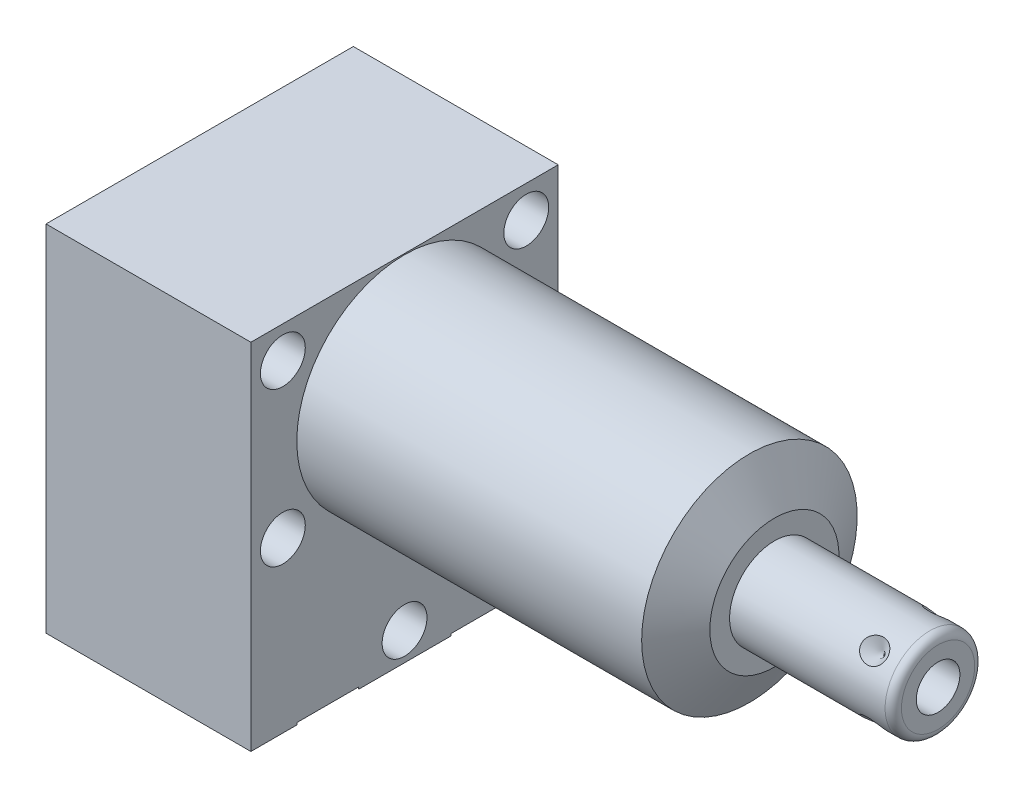
SolidWorks part; units mm, degrees
material "Alloy Steel"
ref_plane "Front Plane" through (0, 0, 0) normal (0, 0, 1) x (1, 0, 0)
ref_plane "Top Plane" through (0, 0, 0) normal (0, 1, 0) x (1, 0, 0)
ref_plane "Right Plane" through (0, 0, 0) normal (1, 0, 0) x (0, 0, -1)
ref_plane "Plane1" through (0, 0, 0) normal (1, 0, 0) x (0, 0, -1)
sketch "Sketch1" plane through (0, 0, 0) normal (1, 0, 0) x (0, 0, -1)
  line L0 (-19.05, 13.4874) -> (-19.05, -30.4546)
  line L1 (-19.05, -30.4546) -> (19.05, -30.4546)
  line L2 (19.05, -30.4546) -> (19.05, 13.4874)
  line L3 (19.05, 13.4874) -> (-19.05, 13.4874)
  line L4 (0, -32.6517) -> (0, 15.6845) construction
  dimension "D1" = 38.1
  dimension "D2" = 43.942
  dimension "D3" = 13.4874
extrude "Extrude1" add sketch "Sketch1" along normal blind 45.847 and the other way blind 25.4
ref_plane "Plane2" through (0, 0, 0) normal (1, 0, 0) x (0, 0, -1)
sketch "Sketch2" plane through (0, 0, 0) normal (1, 0, 0) x (0, 0, -1)
  line L0 (-14.6964, 0) -> (14.6964, 0) construction
  line L5 (19.05, 13.4874) -> (-19.05, 13.4874)
  line L6 (-19.05, 13.4874) -> (-19.05, -30.4546)
  line L7 (-19.05, -30.4546) -> (19.05, -30.4546)
  line L8 (19.05, -30.4546) -> (19.05, 13.4874)
  line L9 (19.05, 13.4874) -> (-19.05, 13.4874)
  line L10 (-19.05, 13.4874) -> (-19.05, -30.4546)
  line L11 (-19.05, -30.4546) -> (19.05, -30.4546)
  line L12 (19.05, -30.4546) -> (19.05, 13.4874)
  circle A0 centre (0, 0) radius 13.3604
  dimension "D1" = 26.7208
  dimension "D2" = 0
extrude "Cut-Extrude1" cut sketch "Sketch2" along normal up to next
ref_plane "Plane3" through (0, 0, 0) normal (0, 0, 1) x (1, 0, 0)
sketch "Sketch3" plane through (0, 0, 0) normal (0, 0, 1) x (1, 0, 0)
  line L0 (42.7527, 13.3604) -> (45.847, 8.001)
  line L1 (42.598, 0) -> (46.0017, 0) construction
  line L2 (45.847, 13.3604) -> (45.847, 8.001)
  line L3 (45.847, 13.3604) -> (42.7527, 13.3604)
  line L4 (45.847, 13.3604) -> (0, 13.3604) construction
  line L5 (45.847, -13.3604) -> (45.847, 13.3604) construction
  dimension "D1" = 30
  dimension "D2" = 16.002
revolve "Cut-Revolve1" cut sketch "Sketch3" angle 360 about L1
ref_plane "Plane4" through (-22.733, -19.8374, 9.525) normal (0, 0, 1) x (0, 1, 0)
sketch "S2D0002" plane through (-22.733, -19.8374, 9.525) normal (0, 0, 1) x (0, 1, 0)
  line L0 (-0.8128, 0) -> (3.7338, 0)
  line L1 (3.7338, 0) -> (3.2938, -2.0701)
  line L2 (3.2938, -2.0701) -> (2.6416, -2.7223)
  line L3 (2.6416, -2.7223) -> (2.6416, -13.97)
  line L4 (2.6416, -13.97) -> (-0.8128, -13.97)
  line L5 (-0.8128, -13.97) -> (-0.8128, 0)
  line L6 (-0.8128, -14.6685) -> (-0.8128, 0.6985) construction
  line L7 (19.8374, -65.4857) -> (19.8374, -22.733) construction
  dimension "D1" = 13.97
  dimension "D2" = 20.6502
revolve "Cut-Revolve2" cut sketch "S2D0002" angle 360 about L6
ref_plane "Plane5" through (-22.733, -19.8374, -9.525) normal (0, 0, 1) x (0, 1, 0)
sketch "Sketch5" plane through (-22.733, -19.8374, -9.525) normal (0, 0, 1) x (0, 1, 0)
  line L0 (-0.8128, 0) -> (3.7338, 0)
  line L1 (3.7338, 0) -> (3.2938, -2.0701)
  line L2 (3.2938, -2.0701) -> (2.6416, -2.7223)
  line L3 (2.6416, -2.7223) -> (2.6416, -13.97)
  line L4 (2.6416, -13.97) -> (-0.8128, -13.97)
  line L5 (-0.8128, -13.97) -> (-0.8128, 0)
  line L6 (-0.8128, -14.6685) -> (-0.8128, 0.6985) construction
  line L7 (19.8374, -65.4857) -> (19.8374, -22.733) construction
  dimension "D1" = 13.97
  dimension "D2" = 20.6502
revolve "Cut-Revolve3" cut sketch "Sketch5" angle 360 about L6
ref_plane "Plane6" through (-8.7376, -30.2006, 9.525) normal (0, 0, 1) x (-1, 0, 0)
sketch "Sketch14" plane through (-25.4, 0, 0) normal (-1, 0, 0) x (0, 0, 1)
  circle A0 centre (-9.525, -20.6502) radius 7.9375
  circle A1 centre (9.525, -20.6502) radius 7.9375
  dimension "D1" = 15.875
extrude "Cut-Extrude2" cut sketch "Sketch14" against normal blind 2.667
sketch "Sketch6" plane through (-8.7376, -30.2006, 9.525) normal (0, 0, 1) x (-1, 0, 0)
  line L0 (16.6624, -43.688) -> (16.6624, 0.254) construction
  line L1 (6.1836, 0) -> (5.641, -2.5527)
  line L2 (5.641, -2.5527) -> (4.9771, -3.2166)
  line L3 (4.9771, -3.2166) -> (4.9771, -17.272)
  line L4 (4.9771, -17.272) -> (0, -17.272)
  line L5 (0, -17.272) -> (0, 0)
  line L6 (0, -18.1356) -> (0, 0.8636) construction
  line L7 (6.1836, 0) -> (9.5237, 0)
  line L8 (9.5237, 0) -> (9.5237, 0.254)
  line L9 (16.6624, 0.254) -> (-8.7376, 0.254) construction
  line L10 (9.5237, 0.254) -> (0, 0.254)
  line L11 (0, 0.254) -> (0, 0)
  dimension "D1" = 19.0475
  dimension "D2" = 0.254
  dimension "D3" = 16.6624
revolve "Cut-Revolve4" cut sketch "Sketch6" angle 360 about L6
ref_plane "Plane7" through (-8.7376, -30.2006, -9.525) normal (0, 0, 1) x (-1, 0, 0)
sketch "Sketch7" plane through (-8.7376, -30.2006, -9.525) normal (0, 0, 1) x (-1, 0, 0)
  line L0 (16.6624, -43.688) -> (16.6624, 0.254) construction
  line L1 (6.1849, 0) -> (5.6423, -2.5527)
  line L2 (5.6423, -2.5527) -> (4.9784, -3.2166)
  line L3 (4.9784, -3.2166) -> (4.9784, -17.272)
  line L4 (4.9784, -17.272) -> (0, -17.272)
  line L5 (0, -17.272) -> (0, 0)
  line L6 (0, -18.1356) -> (0, 0.8636) construction
  line L7 (6.1849, 0) -> (9.5237, 0)
  line L8 (9.5237, 0) -> (-8.7376, 0) construction
  line L9 (9.5237, 0) -> (9.5237, 0.254)
  line L10 (16.6624, 0.254) -> (-8.7376, 0.254) construction
  line L11 (9.5237, 0.254) -> (0, 0.254)
  line L12 (0, 0.254) -> (0, 0)
  dimension "D1" = 16.6624
  dimension "D2" = 9.9568
  dimension "D3" = 19.0475
revolve "Cut-Revolve5" cut sketch "Sketch7" angle 360 about L6
ref_plane "Plane8" through (0, 0, 0) normal (0, 0, 1) x (1, 0, 0)
sketch "Sketch8" plane through (0, 0, 0) normal (0, 0, 1) x (1, 0, 0)
  line L0 (45.847, 0) -> (45.847, 5.5562)
  line L1 (45.847, 5.5562) -> (65.1256, 5.5562)
  line L2 (66.1416, 4.5403) -> (66.1416, 0)
  line L3 (66.1416, 0) -> (45.847, 0)
  line L4 (44.8323, 0) -> (67.1563, 0) construction
  line L5 (45.847, -8.001) -> (45.847, 8.001) construction
  line L6 (-25.4, 13.4874) -> (-25.4, -30.4546) construction
  arc A0 (66.1416, 4.5403) -> (65.1256, 5.5562) centre (65.1256, 4.5403) ccw
  point P0 (45.847, 0)
  dimension "D3" = 1.016
  dimension "D1" = 91.5416
  dimension "D2" = 11.1125
revolve "Revolve1" add sketch "Sketch8" angle 360 about L4
ref_plane "Plane9" through (66.1416, -2.8067, 0) normal (0, 0, 1) x (0, -1, 0)
sketch "S2D0001" plane through (66.1416, -2.8067, 0) normal (0, 0, 1) x (0, -1, 0)
  line L0 (-0.1016, 0) -> (-0.1016, -9.652)
  line L1 (-0.1016, -9.652) -> (-2.8067, -11.2774)
  line L2 (-0.1016, 0) -> (-2.8067, 0)
  line L3 (-2.8067, 0) -> (-2.8067, -11.2774)
  line L4 (-2.8067, -12.4388) -> (-2.8067, 0.5923) construction
  line L5 (1.7335, 0) -> (-7.3469, 0) construction
  dimension "D1" = 5.4102
  dimension "D2" = 9.652
  dimension "D3" = 59
revolve "Cut-Revolve6" cut sketch "S2D0001" angle 360 about L4
ref_plane "Plane10" through (-25.4, -30.2006, 0) normal (0, -1, 0) x (0, 0, -1)
sketch "Sketch10" plane through (-25.4, -30.2006, 0) normal (0, -1, 0) x (0, 0, -1)
  circle A0 centre (-9.525, 16.6624) radius 6.4389
  circle A1 centre (-9.525, 16.6624) radius 6.1836 construction
  dimension "D1" = 12.8778
extrude "Extrude2" add sketch "Sketch10" along normal blind 1.651
sketch "Sketch11" plane through (-22.733, 0, 0) normal (-1, 0, 0) x (0, 0, 1)
  circle A0 centre (9.525, -20.6502) radius 4.8006
  circle A1 centre (9.525, -20.6502) radius 4.5466 construction
  dimension "D1" = 9.6012
ref_plane "Plane11" through (-25.4, 0, 0) normal (1, 0, 0) x (0, 0, -1)
extrude "Extrude3" add sketch "Sketch11" along normal up to surface (2.667 mm away) up to plane "Plane11"
ref_plane "Plane12" through (62.1792, -5.5562, 0) normal (0, 0, 1) x (-1, 0, 0)
ref_plane "Plane13" through (0, 0, 0) normal (0, 0.7071, 0.7071) x (-1, 0, 0)
sketch "Sketch12" plane through (62.1792, 3.9289, -3.9289) normal (0, -0.7071, -0.7071) x (-1, 0, 0)
  line L0 (0, 0) -> (1.5875, 0)
  line L1 (1.5875, 0) -> (0, -1.5875)
  line L2 (0, 0) -> (0, -1.5875)
  line L3 (0, -3.434) -> (0, 0.0794) construction
  line L4 (16.3322, 0) -> (-2.9464, 0) construction
  line L5 (-3.9624, -1.016) -> (-3.9624, -10.0965) construction
  dimension "D1" = 3.9624
  dimension "D2" = 45
  dimension "D3" = 3.175
revolve "Cut-Revolve7" cut sketch "Sketch12" angle 360 about L3
pattern_circular "CirPattern1" count 4 over 360 about axis through (45.848, 0, 0) along (-1, 0, 0) of "Cut-Revolve7"
hole_wizard "Hole1" positions "Sketch17" profile "Sketch16" legacy end condition up to next
sketch "Sketch17" plane through (0, 0, 0) normal (1, 0, 0) x (0, 0, -1)
  line L0 (0, 0) -> (0, 17.9298) construction
  line L1 (0, 0) -> (-24.6425, 0) construction
  point P0 (-15.0876, 9.525)
  point P10 (-15.0876, -9.525)
  point P12 (15.0876, 9.525)
  point P13 (15.0876, -9.525)
  point P14 (0, -26.9748)
  dimension "D1" = 9.525
  dimension "D2" = 15.0876
  dimension "D3" = 26.9748
sketch "Sketch16" plane through (0, 9.525, 15.0876) normal (0, 1, 0) x (0, 0, -1)
  line L0 (0, 0) -> (0, 25.4)
  line L1 (0, 25.4) -> (2.7813, 25.4)
  line L2 (2.7813, 25.4) -> (2.7813, 0)
  line L3 (2.7813, 0) -> (0, 0)
  line L4 (0, 110) -> (0, -10) construction
  dimension "Diameter" = 5.5626
  dimension "Depth" = 25.4
